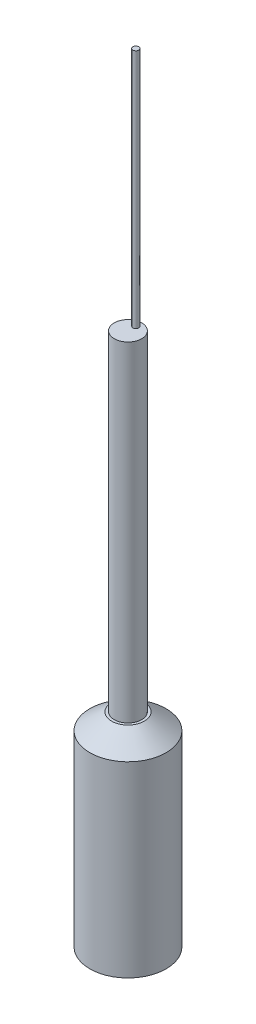
SolidWorks part; units mm, degrees
ref_plane "Front Plane" through (0, 0, 0) normal (0, 0, 1) x (1, 0, 0)
ref_plane "Top Plane" through (0, 0, 0) normal (0, 1, 0) x (1, 0, 0)
ref_plane "Right Plane" through (0, 0, 0) normal (1, 0, 0) x (0, 0, -1)
sketch "Sketch1" plane through (0, 0, 0) normal (0, 1, 0) x (1, 0, 0)
  circle A0 centre (0, 0) radius 5.55
  dimension "D1" = 11.1
extrude "Boss-Extrude1" add sketch "Sketch1" along normal blind 29.62
chamfer "Chamfer1" distance 2.38 distance2 3.175 1 edges at (0, 29.62, 5.55)
sketch "Sketch2" plane through (0, 29.62, 0) normal (0, 1, 0) x (1, 0, 0)
  circle A0 centre (0, 0) radius 2
  dimension "D1" = 4
extrude "Boss-Extrude2" add sketch "Sketch2" along normal blind 48
sketch "Sketch3" plane through (0, 77.62, 0) normal (0, 1, 0) x (1, 0, 0)
  circle A0 centre (0, 1.1433) radius 0.43
  dimension "D1" = 0.86
extrude "Boss-Extrude3" add sketch "Sketch3" along normal blind 35
